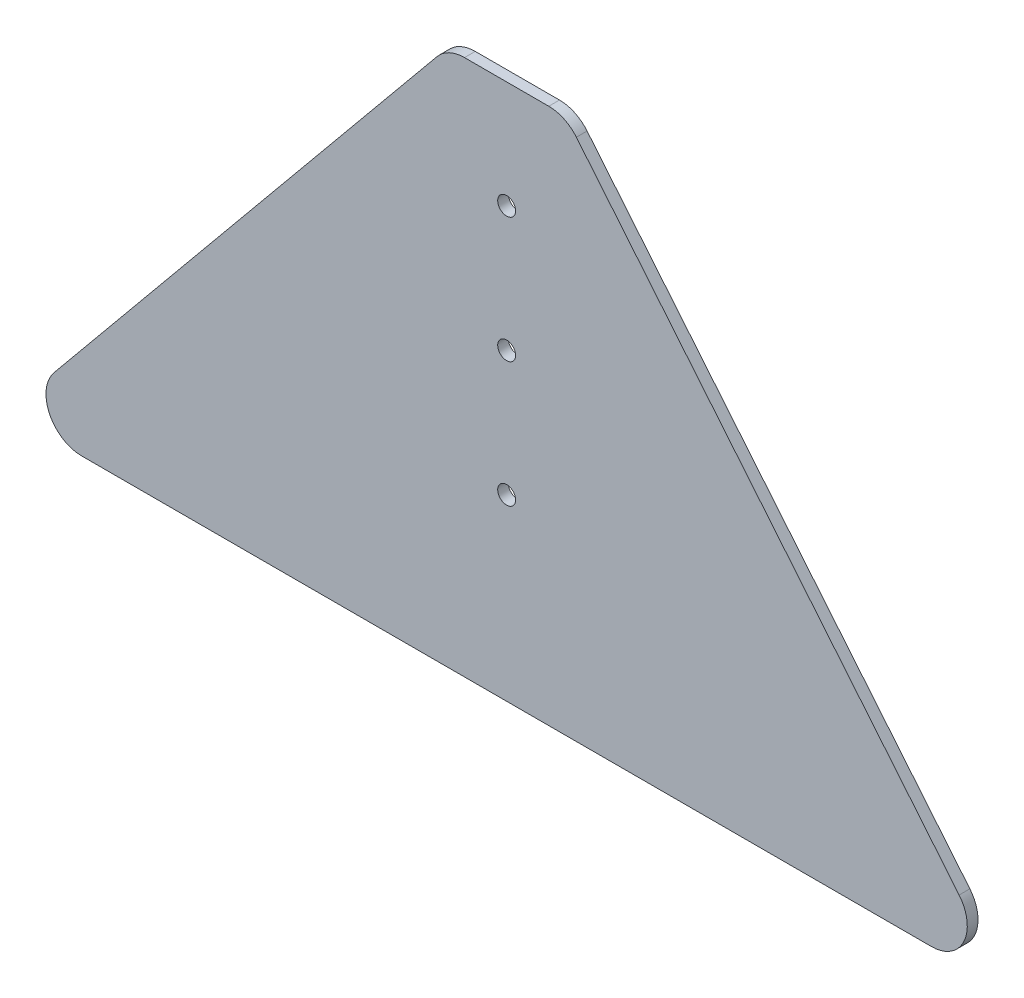
SolidWorks part; units mm, degrees
material "AISI 1020"
ref_plane "Front Plane" through (0, 0, 0) normal (0, 0, 1) x (1, 0, 0)
ref_plane "Top Plane" through (0, 0, 0) normal (0, 1, 0) x (1, 0, 0)
ref_plane "Right Plane" through (0, 0, 0) normal (1, 0, 0) x (0, 0, -1)
sketch "Sketch1" plane through (0, 0, 0) normal (0, 0, 1) x (1, 0, 0)
  line L0 (0, 150) -> (-123.5, 0)
  line L1 (0, 0) -> (33, 0)
  line L2 (0, 0) -> (0, 150) construction
  line L3 (0, 150) -> (33, 150)
  line L4 (33, 0) -> (33, 150) construction
  line L5 (-123.5, 0) -> (0, 0)
  line L6 (16.5, 150) -> (16.5, 0) construction
  line L7 (156.5, 0) -> (33, 0)
  line L8 (33, 150) -> (156.5, 0)
  line L9 (0, 75) -> (33, 75) construction
  circle A0 centre (16.5, 85) radius 2.5
  circle A1 centre (16.5, 120) radius 2.5
  circle A3 centre (16.5, 50) radius 2.5
  dimension "D2" = 5
  dimension "D7" = 5
  dimension "D1" = 150
  dimension "D3" = 35
  dimension "D4" = 280
  dimension "D5" = 33
  dimension "D6" = 50
  dimension "D8" = 35
extrude "Boss-Extrude1" add sketch "Sketch1" along normal blind 3
fillet "Fillet1" radius 10 4 edges at (33, 150, 1.5) (0, 150, 1.5) (-123.5, 0, 1.5) (156.5, 0, 1.5)
